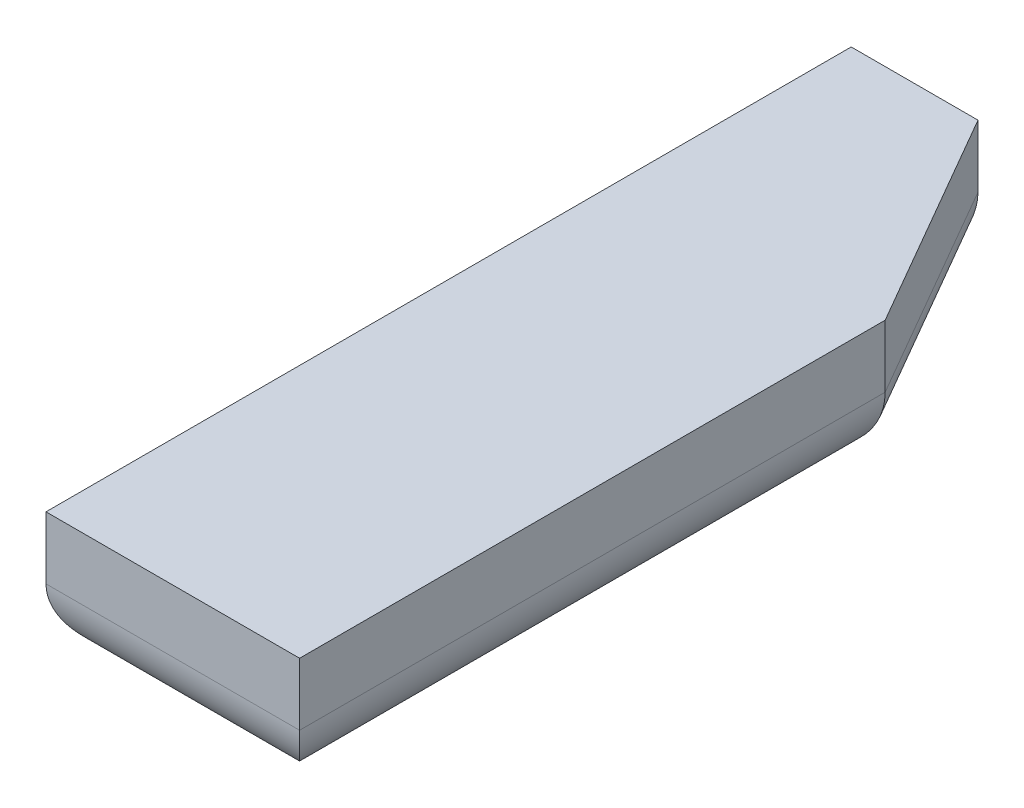
SolidWorks part; units mm, degrees
ref_plane "Front Plane" through (0, 0, 0) normal (0, 0, 1) x (1, 0, 0)
ref_plane "Top Plane" through (0, 0, 0) normal (0, 1, 0) x (1, 0, 0)
ref_plane "Right Plane" through (0, 0, 0) normal (1, 0, 0) x (0, 0, -1)
sketch "Sketch1" plane through (0, 0, 0) normal (0, 1, 0) x (1, 0, 0)
  line L0 (10, -31.75) -> (10, 14.4295)
  line L1 (10, 14.4295) -> (0, 31.75)
  line L2 (-10, 31.75) -> (-10, -31.75)
  line L3 (-10, -31.75) -> (10, -31.75)
  line L4 (0, 31.75) -> (-10, 31.75)
  point P2 (0, -31.75)
  point P12 (-10, 0)
  dimension "D1" = 120
  dimension "D2" = 63.5
  dimension "D3" = 20
extrude "Boss-Extrude1" add sketch "Sketch1" along normal blind 10
fillet "Fillet1" radius 5.08 5 edges at (10, 0, 8.6603) (5, 0, -23.0897) (-5, 0, -31.75) (-10, 0, 0) (0, 0, 31.75)
